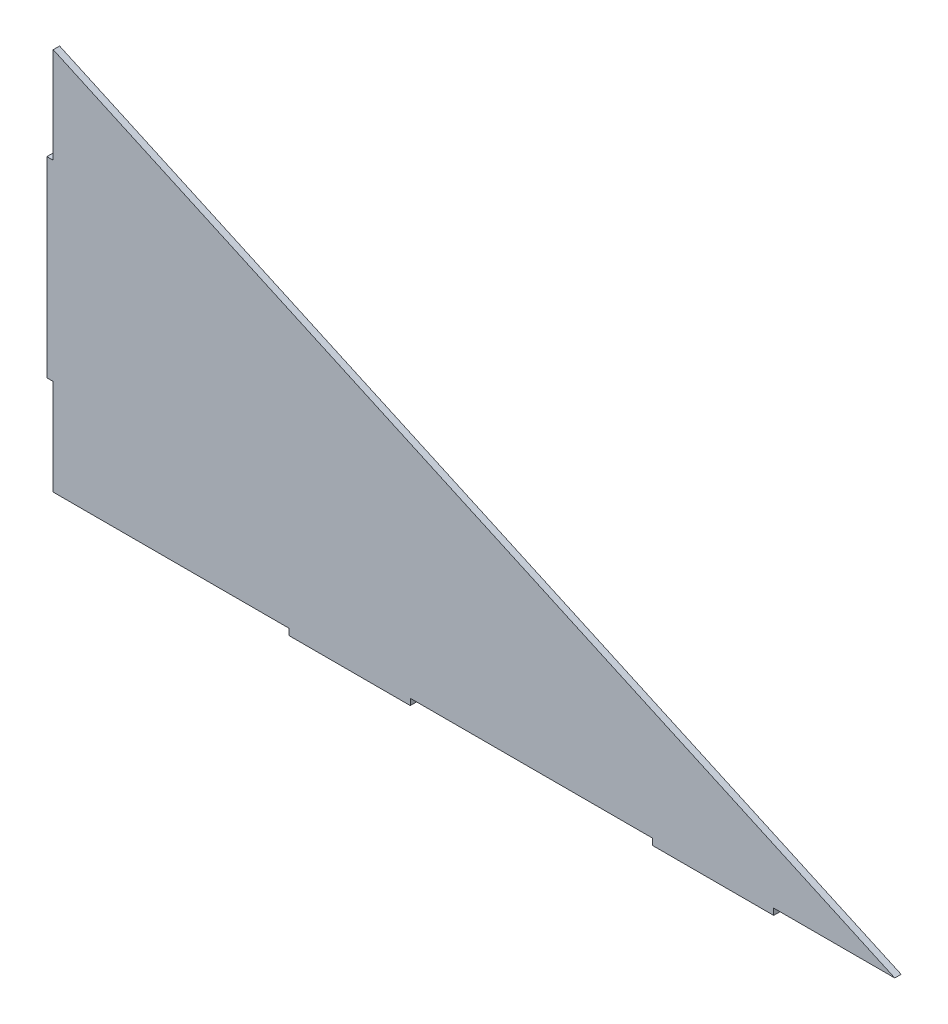
SolidWorks part; units mm, degrees
ref_plane "Plano frontal" through (0, 0, 0) normal (0, 0, 1) x (1, 0, 0)
ref_plane "Plano superior" through (0, 0, 0) normal (0, 1, 0) x (1, 0, 0)
ref_plane "Plano direito" through (0, 0, 0) normal (1, 0, 0) x (0, 0, -1)
sketch "Esboço1" plane through (0, 0, 0) normal (0, 0, 1) x (1, 0, 0)
  line L0 (0, 0) -> (0, 45.1906)
  line L1 (0, 180.7624) -> (397, 0)
  line L2 (397, 0) -> (339.8571, 0)
  line L3 (0, 135.5718) -> (0, 180.7624)
  line L4 (0, 135.5718) -> (-3, 135.5718)
  line L5 (282.7143, 0) -> (168.4286, 0)
  line L6 (0, 45.1906) -> (-3, 45.1906)
  line L7 (-3, 135.5718) -> (-3, 45.1906)
  line L9 (282.7143, 0) -> (282.7143, -3)
  line L10 (282.7143, -3) -> (339.8571, -3)
  line L11 (339.8571, 0) -> (339.8571, -3)
  line L13 (168.4286, 0) -> (168.4286, -3)
  line L14 (168.4286, -3) -> (111.2857, -3)
  line L15 (111.2857, 0) -> (111.2857, -3)
  line L16 (111.2857, 0) -> (0, 0)
  point P16 (0, 0)
  dimension "D1" = 397
  dimension "D2" = 180.7624
  dimension "D3" = 45.1906
  dimension "D4" = 90.3812
  dimension "D5" = 3
  dimension "D6" = 57.1429
  dimension "D7" = 57.1429
  dimension "D8" = 114.2857
  dimension "D9" = 57.1429
  dimension "D10" = 3
extrude "Ressalto-extrusão1" add sketch "Esboço1" along normal blind 3
